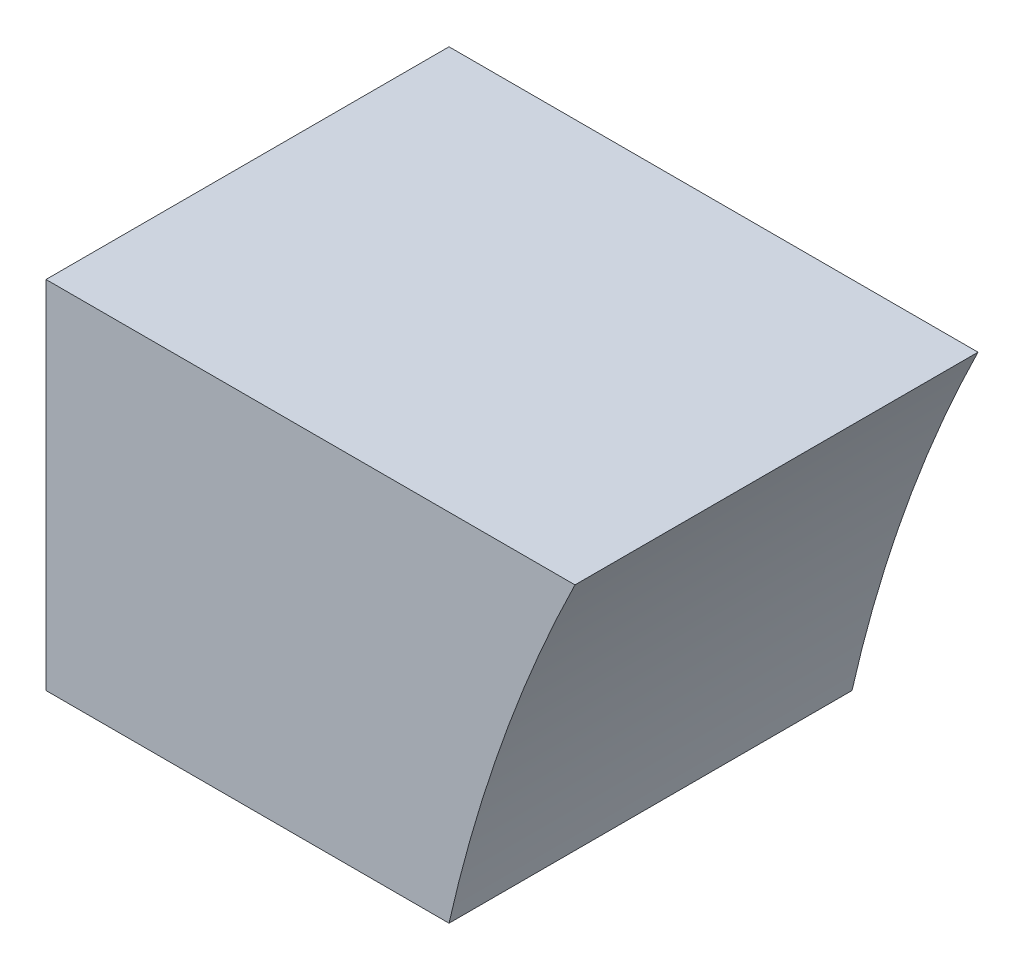
SolidWorks part; units mm, degrees
material "砖"
ref_plane "前视基准面" through (0, 0, 0) normal (0, 0, 1) x (1, 0, 0)
ref_plane "上视基准面" through (0, 0, 0) normal (0, 1, 0) x (1, 0, 0)
ref_plane "右视基准面" through (0, 0, 0) normal (1, 0, 0) x (0, 0, -1)
sketch "草图1" plane through (0, 0, 0) normal (0, 0, 1) x (1, 0, 0)
  line L0 (-4560, 0) -> (-7920, 0)
  line L1 (-12480, 7680) -> (0, 7680)
  line L2 (-12480, 7680) -> (-12480, 0)
  line L3 (-12480, 0) -> (0, 0)
  line L4 (0, 7680) -> (0, 0)
  line L5 (-7920, 0) -> (-7920, 3840)
  line L6 (-7920, 3840) -> (-4560, 3840)
  line L7 (-4560, 3840) -> (-4560, 0)
  line L8 (-7920, 3840) -> (-8160, 3840)
  line L9 (-4560, 3840) -> (-4320, 3840)
  line L10 (-7837.7749, 4359.1486) -> (-8066.0285, 4433.3126)
  line L11 (-7599.1486, 4827.4792) -> (-7793.3126, 4968.5477)
  line L12 (-7227.4792, 5199.1486) -> (-7368.5477, 5393.3126)
  line L13 (-6759.1486, 5437.7749) -> (-6833.3126, 5666.0285)
  line L14 (-6240, 5520) -> (-6240, 5760)
  line L15 (-5720.8514, 5437.7749) -> (-5646.6874, 5666.0285)
  line L16 (-5252.5208, 5199.1486) -> (-5111.4523, 5393.3126)
  line L17 (-4880.8514, 4827.4792) -> (-4686.6874, 4968.5477)
  line L18 (-4642.2251, 4359.1486) -> (-4413.9715, 4433.3126)
  line L19 (-4560, 3840) -> (-4320, 3840)
  line L20 (-4573.7633, 3298.6069) -> (-4560, 3294.1349)
  line L21 (-6833.3126, 5666.0285) -> (-6928.8298, 5960)
  line L22 (-5683.7694, 5551.9017) -> (-5551.1702, 5960)
  line L23 (-5551.1702, 5960) -> (-6928.8298, 5960)
  line L24 (-7920, 0) -> (-9123.3069, 0)
  line L25 (-8160, 0) -> (-8640, 0)
  line L26 (-8160, 0) -> (-8640, 0)
  line L27 (-8640, 3840) -> (-8160, 3840)
  line L28 (-8640, 3840) -> (-8640, 4264)
  line L29 (-7837.7749, 3320.8514) -> (-7920, 3294.1349) [skipped]
  line L30 (-7599.1486, 2852.5208) -> (-7793.3126, 2711.4523) [skipped]
  line L31 (-7227.4792, 2480.8514) -> (-7368.5477, 2286.6874) [skipped]
  line L32 (-6759.1486, 2242.2251) -> (-6833.3126, 2013.9715) [skipped]
  line L33 (-6240, 2160) -> (-6240, 1920) [skipped]
  line L34 (-5720.8514, 2242.2251) -> (-5646.6874, 2013.9715) [skipped]
  line L35 (-5252.5208, 2480.8514) -> (-5111.4523, 2286.6874) [skipped]
  line L36 (-4880.8514, 2852.5208) -> (-4686.6874, 2711.4523) [skipped]
  line L37 (-8640, 4264) -> (-8112.5982, 4264)
  line L38 (-8112.5982, 4264) -> (-8592.5982, 4264)
  line L39 (-8592.5982, 4264) -> (-8592.5982, 4688)
  line L40 (-8592.5982, 4688) -> (-7962.5841, 4688)
  line L41 (-7962.5841, 4688) -> (-8442.5841, 4688)
  line L42 (-8442.5841, 4688) -> (-8442.5841, 5112)
  line L43 (-8442.5841, 5112) -> (-7678.1989, 5112)
  line L44 (-7678.1989, 5112) -> (-8158.1989, 5112)
  line L45 (-8158.1989, 5112) -> (-8158.1989, 5536)
  line L46 (-8158.1989, 5536) -> (-7139.9911, 5536)
  line L47 (-7139.9911, 5536) -> (-7619.9911, 5536)
  line L48 (-7619.9911, 5536) -> (-7619.9911, 5960)
  line L49 (-7619.9911, 5960) -> (-6928.8298, 5960)
  arc A0 (-4560, 3840) -> (-7920, 3840) centre (-6240, 3840) ccw
  arc A1 (-4320, 3840) -> (-8160, 3840) centre (-6240, 3840) ccw
  point P7 (-6240, 0)
  point P56 (-6240, 3840)
  dimension "D5" = 3840
  dimension "D1" = 12480
  dimension "D2" = 7680
  dimension "D3" = 3360
  dimension "D4" = 3840
  dimension "D7" = 240
  dimension "D8" = 480
  dimension "D9" = 424
  dimension "D10" = 720
  dimension "D11" = 480
  dimension "D12" = 480
  dimension "D13" = 480
  dimension "D14" = 480
  dimension "D6" = 20
extrude "凸台-拉伸1" add sketch "草图1" along normal blind 480 contours A1 L40 L39 L37
scale "缩放比例1" scale about origin uniform scaling yes scale factor 1.3
